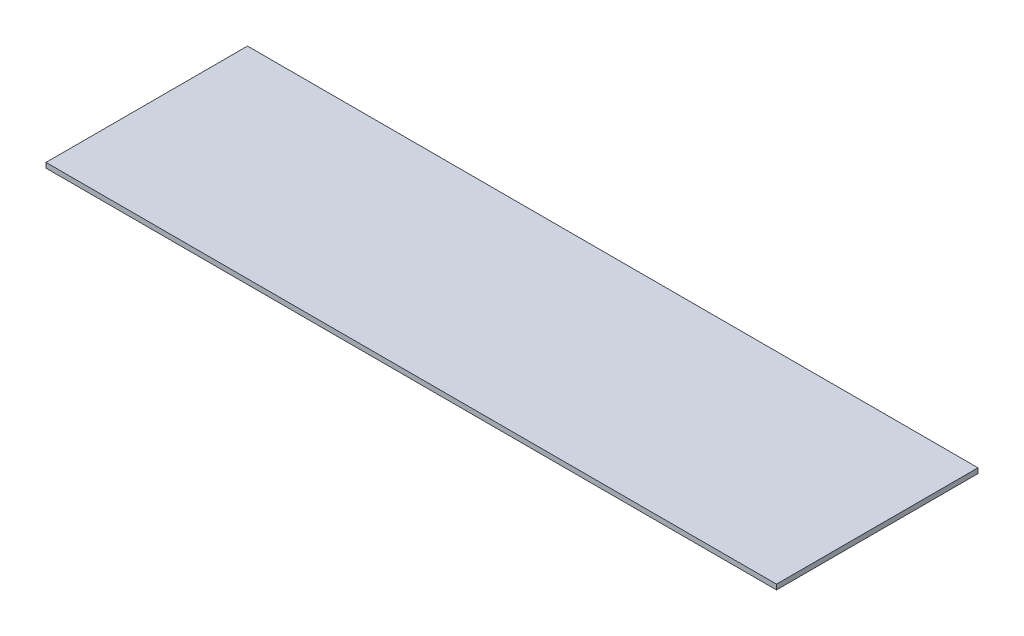
SolidWorks part; units mm, degrees
ref_plane "Front" through (0, 0, 0) normal (0, 0, 1) x (1, 0, 0)
ref_plane "Top" through (0, 0, 0) normal (0, 1, 0) x (1, 0, 0)
ref_plane "Right" through (0, 0, 0) normal (1, 0, 0) x (0, 0, -1)
sketch "Sketch1" plane through (0, 0, 0) normal (0, 1, 0) x (1, 0, 0)
  line L1 (-145, -40) -> (145, -40)
  line L2 (-145, -40) -> (-145, 40)
  line L3 (-145, 40) -> (145, 40)
  line L4 (145, -40) -> (145, 40)
  line L5 (-145, -40) -> (145, 40) construction
  line L6 (-145, 40) -> (145, -40) construction
  point P0 (0, 0)
  dimension "D1" = 80
  dimension "D2" = 290
extrude "Boss-Extrude1" add sketch "Sketch1" along normal blind 2
